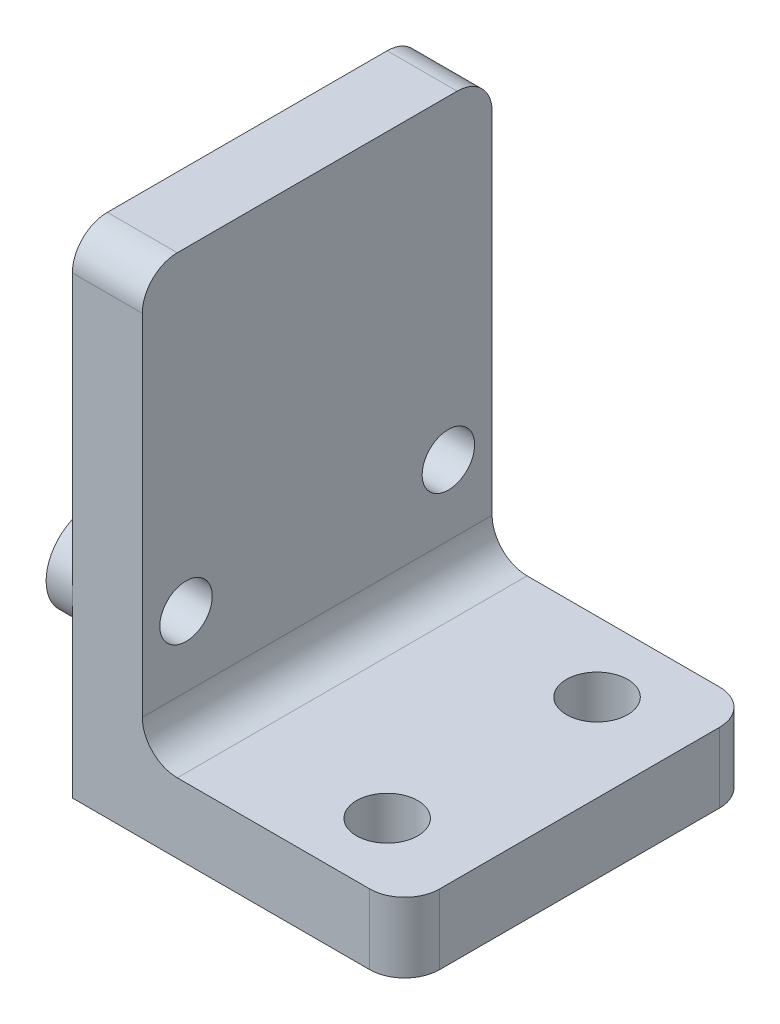
SolidWorks part; units mm, degrees
ref_plane "Front Plane" through (0, 0, 0) normal (0, 0, 1) x (1, 0, 0)
ref_plane "Top Plane" through (0, 0, 0) normal (0, 1, 0) x (1, 0, 0)
ref_plane "Right Plane" through (0, 0, 0) normal (1, 0, 0) x (0, 0, -1)
sketch "Sketch1" plane through (0, 0, 0) normal (0, 0, 1) x (1, 0, 0)
  line L0 (0, 0) -> (0, 28)
  line L1 (0, 28) -> (4, 28)
  line L2 (4, 28) -> (4, 4)
  line L3 (4, 4) -> (19, 4)
  line L4 (19, 4) -> (19, 0)
  line L5 (19, 0) -> (0, 0)
  dimension "D1" = 4
  dimension "D2" = 4
  dimension "D3" = 24
  dimension "D4" = 15
extrude "Boss-Extrude1" add sketch "Sketch1" along normal blind 20
sketch "Sketch2" plane through (0, 0, 0) normal (-1, 0, 0) x (0, 0, 1)
  line L0 (20, 28) -> (0, 28) construction
  line L1 (20, 28) -> (20, 0) construction
  circle A0 centre (17.5, 10) radius 1.5
  circle A1 centre (2.5, 10) radius 1.5
  dimension "D2" = 3
  dimension "D1" = 15
  dimension "D3" = 18
  dimension "D4" = 2.5
extrude "Cut-Extrude1" cut sketch "Sketch2" against normal through all
sketch "Sketch3" plane through (0, 4, 0) normal (0, 1, 0) x (1, 0, 0)
  line L0 (19, -20) -> (19, 0) construction
  circle A0 centre (14, -4) radius 1.75
  circle A1 centre (14, -16) radius 1.75
  point P6 (19, -10)
  dimension "D1" = 3.5
  dimension "D2" = 3.5
  dimension "D3" = 12
  dimension "D4" = 6
  dimension "D5" = 5
extrude "Cut-Extrude2" cut sketch "Sketch3" against normal through all
fillet "Fillet1" radius 2 5 edges at (19, 2, 0) (19, 2, 20) (4, 4, 10) (2, 28, 0) (2, 28, 20)
sketch "Sketch4" plane through (0, 0, 0) normal (-1, 0, 0) x (0, 0, 1)
  circle A0 centre (2.5, 10) radius 2.5
  circle A1 centre (17.5, 10) radius 2.5
  circle A2 centre (17.5, 10) radius 1.5 construction
  circle A3 centre (2.5, 10) radius 1.5 construction
  circle A4 centre (17.5, 10) radius 1.5
  circle A5 centre (2.5, 10) radius 1.5
extrude "Boss-Extrude2" add sketch "Sketch4" along normal blind 1.5
